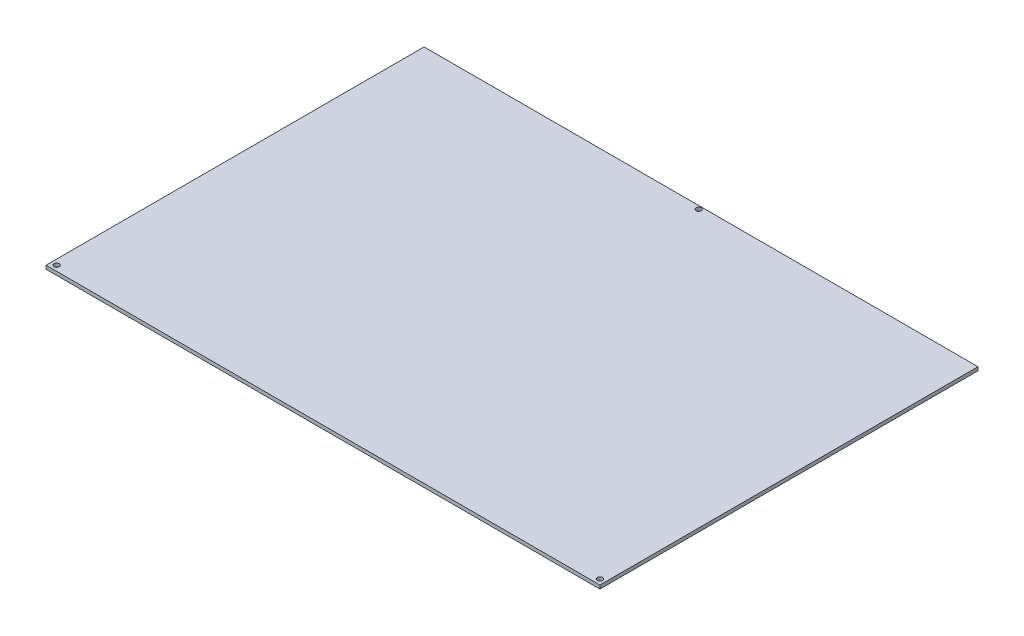
SolidWorks part; units mm, degrees
ref_plane "Front Plane" through (0, 0, 0) normal (0, 0, 1) x (1, 0, 0)
ref_plane "Top Plane" through (0, 0, 0) normal (0, 1, 0) x (1, 0, 0)
ref_plane "Right Plane" through (0, 0, 0) normal (1, 0, 0) x (0, 0, -1)
sketch "Sketch1" plane through (0, 0, 0) normal (0, 1, 0) x (1, 0, 0)
  line L1 (0, 0) -> (315, 0)
  line L2 (0, 0) -> (0, 215)
  line L3 (0, 215) -> (315, 215)
  line L4 (315, 0) -> (315, 215)
  dimension "D1" = 215
  dimension "D2" = 315
extrude "Boss-Extrude1" add sketch "Sketch1" along normal blind 2
sketch "Sketch2" plane through (0, 2, 0) normal (0, 1, 0) x (1, 0, 0)
  line L0 (0, 0) -> (315, 0) construction
  line L1 (0, 215) -> (0, 0) construction
  line L2 (315, 0) -> (315, 215) construction
  circle A0 centre (3, 3) radius 1.5
  circle A1 centre (312, 3) radius 1.5
  dimension "D3" = 3
  dimension "D4" = 3
  dimension "D1" = 3
  dimension "D2" = 3
  dimension "D5" = 3
  dimension "D6" = 3
extrude "Cut-Extrude1" cut sketch "Sketch2" against normal blind 47
sketch "Sketch3" plane through (0, 2, 0) normal (0, 1, 0) x (1, 0, 0)
  line L0 (0, 215) -> (0, 0) construction
  circle A0 centre (158, 213.1171) radius 1.5
  dimension "D1" = 3
  dimension "D2" = 158
extrude "Cut-Extrude2" cut sketch "Sketch3" against normal blind 47
